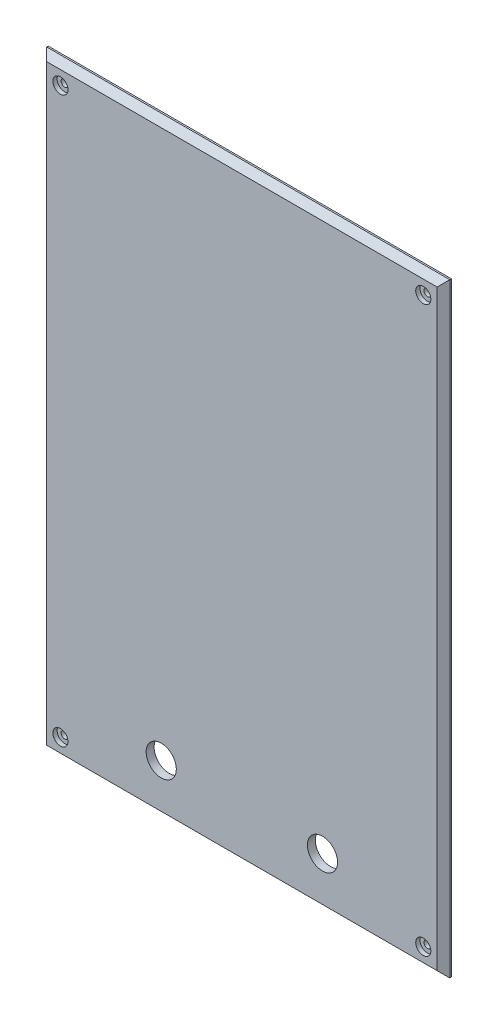
SolidWorks part; units mm, degrees
ref_plane "Front Plane" through (0, 0, 0) normal (0, 0, 1) x (1, 0, 0)
ref_plane "Top Plane" through (0, 0, 0) normal (0, 1, 0) x (1, 0, 0)
ref_plane "Right Plane" through (0, 0, 0) normal (1, 0, 0) x (0, 0, -1)
sketch "Sketch1" plane through (0, 0, 0) normal (0, 0, 1) x (1, 0, 0)
  line L0 (0, 0) -> (0, 176.6487) construction
  line L1 (-127, 190.5) -> (127, 190.5)
  line L2 (-127, 190.5) -> (-127, -190.5)
  line L3 (-127, -190.5) -> (127, -190.5)
  line L4 (127, 190.5) -> (127, -190.5)
  line L5 (-63.0006, 0) -> (126.0012, 0) construction
  dimension "D1" = 381
  dimension "D2" = 254
extrude "Boss-Extrude1" add sketch "Sketch1" along normal blind 5
chamfer "Chamfer1" distance 4 angle 45 4 edges at (-127, 0, 5) (0, -190.5, 5) (127, 0, 5) (0, 190.5, 5)
hole_wizard "CBORE for #8 Binding Head Machine Screw1" positions "Sketch3" profile "Sketch2" counterbore size "#8" standard "ANSI Inch" end condition through all
sketch "Sketch3" plane through (0, 0, 5) normal (0, 0, 1) x (1, 0, 0)
  line L0 (-127, 190.5) -> (127, 190.5) construction
  line L1 (-127, 190.5) -> (-127, -190.5) construction
  point P0 (-114.3, 177.8)
  dimension "D1" = 12.7
  dimension "D2" = 12.7
sketch "Sketch2" plane through (-114.3, 177.8, 5) normal (1, 0, 0) x (0, -1, 0)
  line L0 (0, 0) -> (0, 5)
  line L1 (0, 5) -> (2.2479, 5)
  line L3 (2.2479, 5) -> (2.2479, 2.667)
  line L4 (2.2479, 2.667) -> (4.7625, 2.667)
  line L5 (4.7625, 2.667) -> (4.7625, 0)
  line L7 (4.7625, 0) -> (0, 0)
  line L11 (0, -6.35) -> (0, 107.95) construction
  dimension "Thru Hole Dia." = 4.4958
  dimension "Thru Hole Depth" = 5
  dimension "C'Bore Dia." = 9.525
  dimension "C'Bore Depth" = 2.667
pattern_linear "LPattern1" count 2 spacing 355.6 along (0, -1, 0) count 2 spacing 228.6 along (1, 0, 0) of "CBORE for #8 Binding Head Machine Screw1"
hole_wizard "Ø19.0 (19) Diameter Hole1" positions "Sketch5" profile "Sketch4" hole size "Ø19.0" standard "ANSI Metric" end condition through all
sketch "Sketch5" plane through (0, 0, 5) normal (0, 0, 1) x (1, 0, 0)
  line L0 (0, 0) -> (0, -88.2741) construction
  line L3 (127, -190.5) -> (-127, -190.5) construction
  point P0 (-50.8, -158.75)
  point P2 (50.8, -158.75)
  dimension "D1" = 31.75
sketch "Sketch4" plane through (-50.8, -158.75, 5) normal (1, 0, 0) x (0, -1, 0)
  line L0 (0, 0) -> (0, 5)
  line L1 (0, 5) -> (9.5, 5)
  line L2 (9.5, 5) -> (9.5, 0)
  line L5 (9.5, 0) -> (0, 0)
  line L11 (0, -6.35) -> (0, 107.95) construction
  dimension "Thru Hole Dia." = 19
  dimension "Thru Hole Depth" = 5
